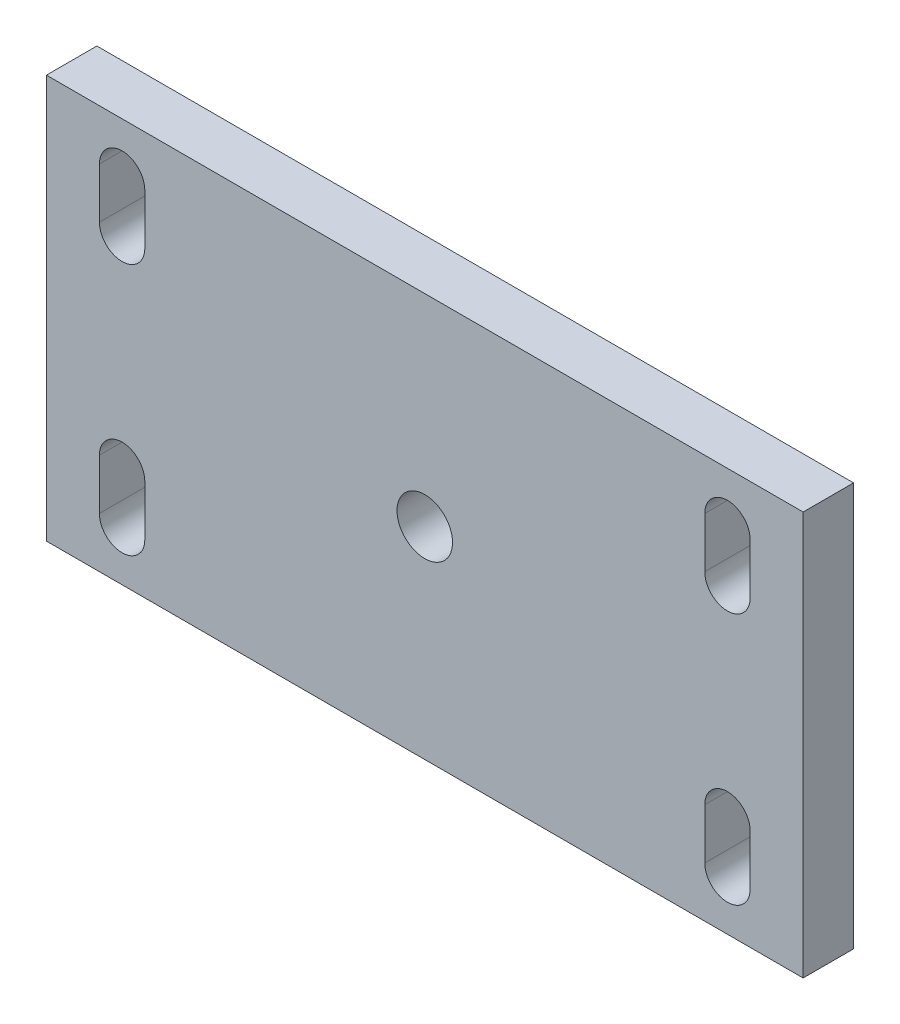
SolidWorks part; units mm, degrees
ref_plane "前视基准面" through (0, 0, 0) normal (0, 0, 1) x (1, 0, 0)
ref_plane "上视基准面" through (0, 0, 0) normal (0, 1, 0) x (1, 0, 0)
ref_plane "右视基准面" through (0, 0, 0) normal (1, 0, 0) x (0, 0, -1)
sketch "草图1" plane through (0, 0, 0) normal (0, 0, 1) x (1, 0, 0)
  line L0 (0, 0) -> (0, 23.9514) construction
  line L1 (-75, 40) -> (75, 40)
  line L2 (-75, 40) -> (-75, -40)
  line L3 (-75, -40) -> (75, -40)
  line L4 (75, 40) -> (75, -40)
  line L5 (-75, 40) -> (75, -40) construction
  line L6 (-75, -40) -> (75, 40) construction
  line L7 (-133.554, 0) -> (85.9905, 0) construction
  line L8 (-60, -20) -> (-60, -30) construction
  line L9 (-55.5, -20) -> (-55.5, -30)
  line L10 (-64.5, -20) -> (-64.5, -30)
  line L11 (-60, 20) -> (-60, 30) construction
  line L12 (-55.5, 20) -> (-55.5, 30)
  line L13 (-64.5, 20) -> (-64.5, 30)
  line L14 (60, -20) -> (60, -30) construction
  line L15 (55.5, -20) -> (55.5, -30)
  line L16 (64.5, -20) -> (64.5, -30)
  line L17 (60, 20) -> (60, 30) construction
  line L18 (55.5, 20) -> (55.5, 30)
  line L19 (64.5, 20) -> (64.5, 30)
  arc A4 (-55.5, -20) -> (-64.5, -20) centre (-60, -20) ccw
  arc A5 (-64.5, -30) -> (-55.5, -30) centre (-60, -30) ccw
  arc A6 (-55.5, 20) -> (-64.5, 20) centre (-60, 20) cw
  arc A7 (-64.5, 30) -> (-55.5, 30) centre (-60, 30) cw
  arc A8 (55.5, -20) -> (64.5, -20) centre (60, -20) cw
  arc A9 (64.5, -30) -> (55.5, -30) centre (60, -30) cw
  arc A10 (55.5, 20) -> (64.5, 20) centre (60, 20) ccw
  arc A11 (64.5, 30) -> (55.5, 30) centre (60, 30) ccw
  point P0 (0, 0)
  point P10 (-60, -25)
  point P19 (-60, 25)
  point P26 (60, -25)
  point P33 (60, 25)
  point P38 (0, 0)
  point P39 (0, 0)
  dimension "D3" = 50
  dimension "D1" = 150
  dimension "D2" = 80
  dimension "D4" = 10
  dimension "D5" = 9
  dimension "D6" = 120
extrude "凸台-拉伸1" add sketch "草图1" along normal blind 10
hole_wizard "大小mm 暗销孔1" positions "3D草图1" profile "草图2" hole size "Ø1.0" standard "GB"
sketch3d "3D草图1"
  point P0 (0, 0, 0)
  point P3 (0, 0, 0)
  point P5 (0, 0, 0)
  point P7 (0, 0, 0)
  point P10 (0, 0, 0)
  point P13 (0, 0, 0)
  dimension "D1" = 0
sketch "草图2" plane through (0, 0, 0) normal (1, 0, 0) x (0, 1, 0)
  line L0 (0, 0) -> (0, 27.8047)
  line L1 (0, 27.8047) -> (5.5, 24.5)
  line L2 (5.5, 24.5) -> (5.5, 0)
  line L5 (5.5, 0) -> (0, 0)
  line L10 (0, 27.8047) -> (-5.5, 24.5) construction
  line L11 (0, -6.35) -> (0, 107.95) construction
  dimension "孔直径" = 11
  dimension "孔深度" = 24.5
  dimension "导头角度" = 118
ref_plane "基准面1" through (0, 0, 0) normal (-1, 0, 0) x (0, 0, 1)
